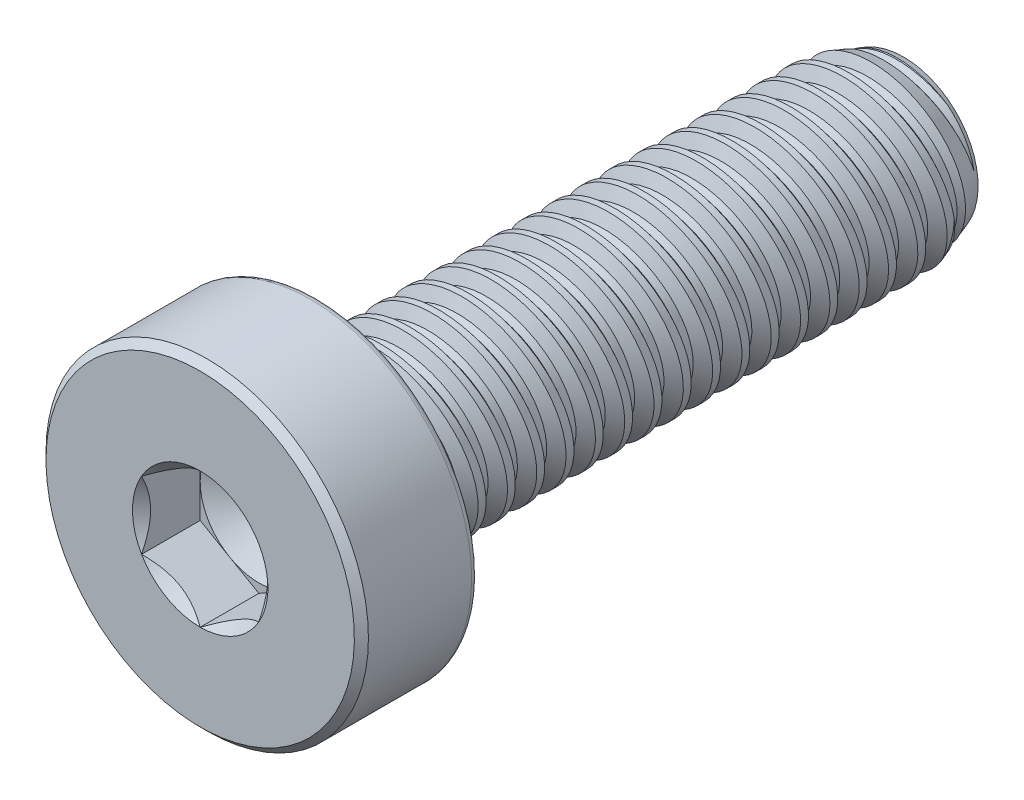
SolidWorks part; units mm, degrees
ref_plane "Front" through (0, 0, 0) normal (0, 0, 1) x (1, 0, 0)
ref_plane "Top" through (0, 0, 0) normal (0, 1, 0) x (1, 0, 0)
ref_plane "Right" through (0, 0, 0) normal (1, 0, 0) x (0, 0, -1)
sketch "Sketch1" plane through (0, 0, 0) normal (1, 0, 0) x (0, 0, -1)
  line L0 (0, 0) -> (-2, 0) construction
  line L1 (0, 0) -> (10, 0)
  line L2 (0, 0) -> (0, 1.5)
  line L3 (0, 1.5) -> (10, 1.5)
  line L4 (10, 0) -> (10, 1.5)
  line L5 (0, -1.5) -> (10, -1.5) construction
  line L6 (-2, 2.75) -> (-2, -2.75) construction
  line L7 (-2, 0) -> (-4, 0) construction
  dimension "Thread Dia" = 3
  dimension "Min Thread Length" = 10
  dimension "Head Height" = 2
  dimension "Head Dia" = 5.5
revolve "Revolve1" add sketch "Sketch1" angle 360 about L0
sketch "Sketch2" plane through (0, 0, 0) normal (1, 0, 0) x (0, 0, -1)
  line L0 (0, 1.5) -> (0, -1.5) construction
  line L1 (0, -1.5) -> (0.5, -1.5) construction
  line L2 (0.5, -1.5) -> (0, 1.5) construction
  line L3 (0, 1.5) -> (0.0616, 1.5103) construction
  line L4 (0.0616, 1.5103) -> (0.4932, 1.5822)
  line L5 (0.4932, 1.5822) -> (0.3836, 1.2896)
  line L6 (0.3836, 1.2896) -> (0.2603, 1.269)
  line L7 (0.2603, 1.269) -> (0.0616, 1.5103)
  line L8 (0.3219, 1.2793) -> (0.2774, 1.5462) construction
  line L9 (0, -1.5) -> (10, -1.5) construction
  line L10 (0, 1.5) -> (10, 1.5) construction
  line L12 (0.2851, 1.5) -> (0.7851, -1.5) construction
  line L13 (0, -0.0892) -> (1.0703, 0.0892) construction
  line L15 (0, 0) -> (0, 1.5) construction
  point P19 (0.5351, 0)
  dimension "D1" = 60
  dimension "Thread Pitch" = 0.5
  dimension "D2" = 0.0625
  dimension "D3" = 0.125
  dimension "D4" = 0.5
revolve "Cut-Revolve1" cut sketch "Sketch2" angle 360 about L13
sketch "Sketch3" plane through (0, 0, 0) normal (1, 0, 0) x (0, 0, -1)
  line L0 (10, 1.269) -> (9.3654, 1.5)
  line L1 (9.3654, 1.5) -> (10, 1.5)
  line L2 (10, 1.5) -> (10, 1.269)
  line L3 (0, 1.5) -> (10, 1.5) construction
  line L4 (10, 0) -> (10, 1.5) construction
  line L5 (9.3654, 0) -> (0, 0) construction
  line L6 (9.3654, 1.5) -> (9.3654, -1.5) construction
  line L7 (0, -1.5) -> (10, -1.5) construction
  dimension "D1" = 20
  dimension "D2" = 3
revolve "Cut-Revolve2" cut sketch "Sketch3" angle 360 about L5
pattern_linear "LPattern1" count 20 spacing 0.5 along (0, 0, 1) count 2 spacing 0.5 along (0, 0, 1)
ref_plane "Plane1" through (0, 0, 0) normal (0, 0, 1) x (1, 0, 0)
sketch "Sketch4" plane through (0, 0, 0) normal (0, 0, 1) x (1, 0, 0)
  circle A0 centre (0, 0) radius 2.75
  dimension "D1" = 5.5
extrude "Extrude1" add sketch "Sketch4" along normal up to vertex
sketch "Sketch10" plane through (0, 0, 0) normal (1, 0, 0) x (0, 0, -1)
  line L0 (-2, 2.63) -> (-1.88, 2.75)
  line L1 (-1.88, 2.75) -> (-0.12, 2.75)
  line L2 (0, 2.63) -> (0.1, 2.63)
  line L3 (0.1, 2.63) -> (0.1, 2.85)
  line L4 (0.1, 2.85) -> (-2, 2.85)
  line L5 (-2, 2.85) -> (-2, 2.63)
  line L7 (0, 2.75) -> (-2, 2.75) construction
  line L9 (0, 2.63) -> (-2, 2.63) construction
  line L10 (-2, 0) -> (-4, 0) construction
  line L11 (0, -2.75) -> (0, 2.75) construction
  line L12 (-2, 2.75) -> (-2, -2.75) construction
  arc A0 (-0.12, 2.75) -> (0, 2.63) centre (-0.12, 2.63) cw
  dimension "D1" = 45
  dimension "D2" = 0.1
  dimension "D3" = 0.1
  dimension "D4" = 0.12
  dimension "D5" = 2
  dimension "D6" = 10
revolve "Cut-Revolve3" cut sketch "Sketch10" angle 360 about L10
sketch "Sketch6" plane through (0, 0, 2) normal (0, 0, 1) x (1, 0, 0)
  line L1 (0, -1.1547) -> (1, -0.5774)
  line L2 (1, -0.5774) -> (1, 0.5774)
  line L3 (1, 0.5774) -> (0, 1.1547)
  line L4 (0, 1.1547) -> (-1, 0.5774)
  line L5 (-1, 0.5774) -> (-1, -0.5774)
  line L6 (-1, -0.5774) -> (0, -1.1547)
  circle A0 centre (0, 0) radius 1 construction
  dimension "Hex" = 2
extrude "Cut-Extrude1" cut sketch "Sketch6" against normal blind 1
sketch "Sketch7" plane through (0, 0, 2) normal (0, 0, 1) x (1, 0, 0)
  circle A0 centre (0, 0) radius 1.1547
extrude "Cut-Extrude4" cut sketch "Sketch7" against normal blind 1 draft 45
sketch "Sketch8" plane through (0, 0, 1) normal (0, 0, 1) x (1, 0, 0)
  circle A0 centre (0, 0) radius 1 construction
  circle A1 centre (0, 0) radius 1
extrude "Cut-Extrude5" cut sketch "Sketch8" against normal blind 0.3333 draft 60
equation "\"D2@Sketch2\"=\"Thread Pitch@Sketch2\"/8"
equation "\"D3@Sketch2\"=\"Thread Pitch@Sketch2\"/4"
equation "\"D4@Sketch2\"=\"Thread Pitch@Sketch2\""
equation "\"D3@LPattern1\"=\"Thread Pitch@Sketch2\""
equation "\"D1@Cut-Extrude4\"=\"D1@Cut-Extrude1\""
equation "\"D1@Cut-Extrude5\"=\"D1@Cut-Extrude1\"/3"
equation "\"D1@LPattern1\"=\"Min Thread Length@Sketch1\"/\"Thread Pitch@Sketch2\""
equation "\"D4@LPattern1\"=\"Thread Pitch@Sketch2\""
equation "\"D4@Sketch10\"=\"Thread Dia@Sketch1\"/25"
equation "\"D1@Cut-Extrude1\"=\"Head Height@Sketch1\"/2"
